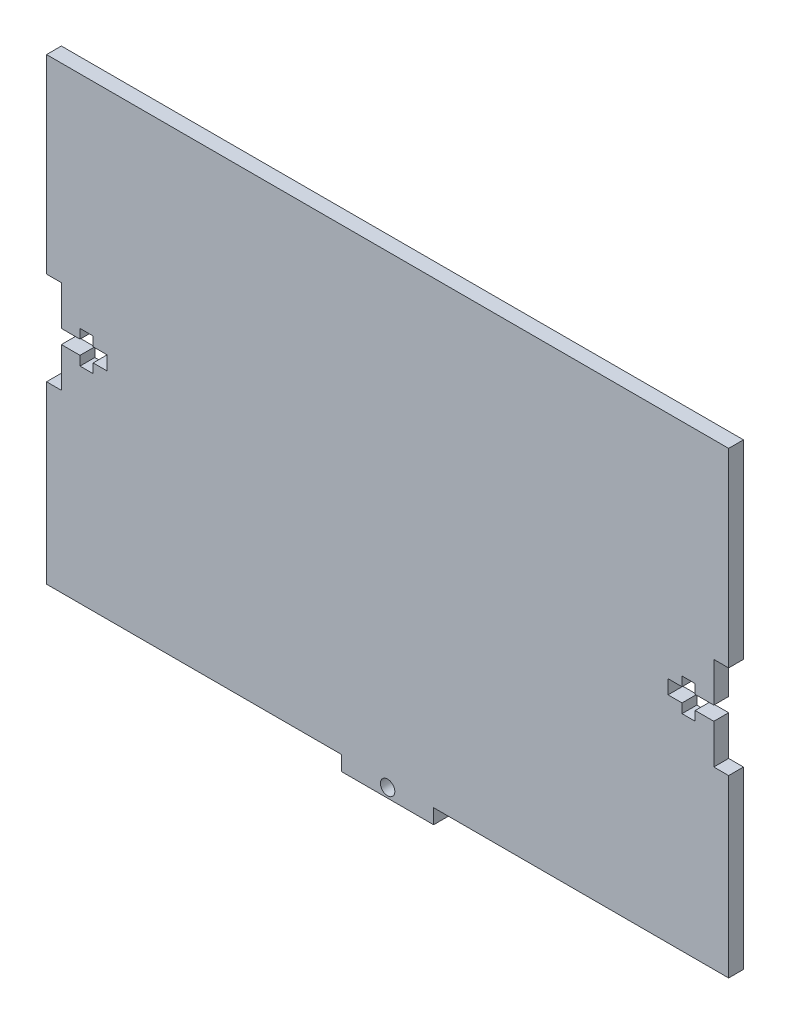
SolidWorks part; units mm, degrees
ref_plane "Front Plane" through (0, 0, 0) normal (0, 0, 1) x (1, 0, 0)
ref_plane "Top Plane" through (0, 0, 0) normal (0, 1, 0) x (1, 0, 0)
ref_plane "Right Plane" through (0, 0, 0) normal (1, 0, 0) x (0, 0, -1)
sketch "Sketch1" plane through (0, 0, 0) normal (0, 0, 1) x (1, 0, 0)
  line L1 (-73.18, 50.8) -> (73.18, 50.8)
  line L2 (-73.18, 50.8) -> (-73.18, -50.8)
  line L3 (-73.18, -50.8) -> (73.18, -50.8)
  line L4 (73.18, 50.8) -> (73.18, -50.8)
  point P0 (0, 0)
  dimension "D1" = 146.36
  dimension "D2" = 101.6
  dimension "D3" = 73.18
  dimension "D4" = 50.8
extrude "Boss-Extrude1" add sketch "Sketch1" along normal blind 3.18
sketch "Sketch2" plane through (0, 0, 3.18) normal (0, 0, 1) x (1, 0, 0)
  line L0 (0, 0) -> (50000, 0) construction
  line L1 (73.18, -50.8) -> (73.18, 50.8) construction
  line L2 (-73.18, 50.8) -> (-73.18, -50.8) construction
  line L3 (-73.18, 10) -> (-70, 10)
  line L4 (-73.18, 10) -> (-73.18, -10)
  line L5 (-73.18, -10) -> (-70, -10)
  line L6 (-70, 10) -> (-70, -10)
  line L8 (-73.18, 1.5) -> (-60.18, 1.5)
  line L9 (-73.18, 1.5) -> (-73.18, -1.5)
  line L10 (-73.18, -1.5) -> (-60.18, -1.5)
  line L11 (-60.18, 1.5) -> (-60.18, -1.5)
  line L12 (-66, 3.5) -> (-63.18, 3.5)
  line L13 (-66, 3.5) -> (-66, -3.5)
  line L14 (-66, -3.5) -> (-63.18, -3.5)
  line L15 (-63.18, 3.5) -> (-63.18, -3.5)
  point P5 (73.18, 0)
  point P20 (-70, 0)
  line M16 (-73.18, 50.8) -> (-73.18, -50.8)
  dimension "D1" = 20
  dimension "D2" = 3.18
  dimension "D3" = 10
  dimension "D4" = 1.5
  dimension "D5" = 3
  dimension "D6" = 13
  dimension "D7" = 2.82
  dimension "D8" = 7
  dimension "D9" = 3.5
  dimension "D10" = 4
extrude "Cut-Extrude1" cut sketch "Sketch2" against normal through all both and the other way through all contours L8 L6 L3 M16 | L4 L0 L6 L8 | L0 L9 L10 L6 | L10 L5 L6 M16 | L6 L0 L13 L8 | L0 L6 L10 L13 | L15 L12 L13 L8 | L13 L0 L15 L8 | L0 L13 L10 L15 | L15 L10 L13 L14 | L15 L0 L11 L8 | L0 L15 L10 L11
mirror "Mirror1" about plane through (0, 0, 0) normal (1, 0, 0) of "Cut-Extrude1"
sketch "Sketch3" plane through (0, 0, 3.18) normal (0, 0, 1) x (1, 0, 0)
  line L0 (0, 0) -> (0, -50000) construction
  line L7 (-73.18, -50.8) -> (-9.875, -50.8)
  line L8 (-73.18, -50.8) -> (-73.18, -47.62)
  line L9 (-73.18, -47.62) -> (-9.875, -47.62)
  line L10 (-9.875, -50.8) -> (-9.875, -47.62)
  dimension "D1" = 63.305
  dimension "D2" = 3.18
extrude "Cut-Extrude2" cut sketch "Sketch3" against normal through all both and the other way through all
mirror "Mirror2" about plane through (0, 0, 0) normal (1, 0, 0) of "Cut-Extrude2"
sketch "Sketch4" plane through (0, 0, 3.18) normal (0, 0, 1) x (1, 0, 0)
  line L0 (-9.875, -50.8) -> (9.875, -50.8) construction
  circle A0 centre (0, -48.8) radius 1.55
  dimension "D1" = 3.1
  dimension "D2" = 2
  dimension "D3" = 9.875
extrude "Cut-Extrude3" cut sketch "Sketch4" against normal through all both and the other way through all contours A0
